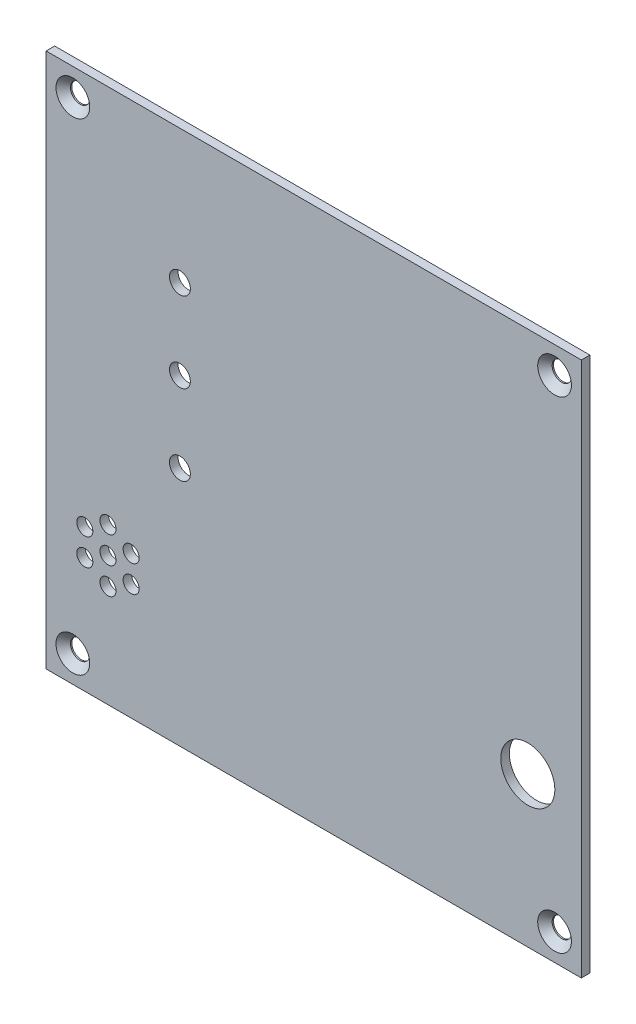
SolidWorks part; units mm, degrees
material "Perspex (TM) Plaque acrylique coulée"
ref_plane "Plan de face" through (0, 0, 0) normal (0, 0, 1) x (1, 0, 0)
ref_plane "Plan de dessus" through (0, 0, 0) normal (0, 1, 0) x (1, 0, 0)
ref_plane "Plan de droite" through (0, 0, 0) normal (1, 0, 0) x (0, 0, -1)
sketch "Esquisse1" plane through (0, 0, 0) normal (0, 0, 1) x (1, 0, 0)
  line L1 (0, 0) -> (100, 0)
  line L2 (0, 0) -> (0, 100)
  line L3 (0, 100) -> (100, 100)
  line L4 (100, 0) -> (100, 100)
  dimension "D1" = 100
  dimension "D2" = 100
extrude "Boss.-Extru.1" add sketch "Esquisse1" along normal blind 1.6
hole_wizard "Fraisage pour vis à tête fraisée M31" positions "Esquisse3D1" profile "Esquisse3" countersink size "M3" standard "ISO" end condition through all
sketch3d "Esquisse3D1"
  line L0 (100, 100, 1.6) -> (0, 100, 1.6) construction
  line L1 (0, 100, 1.6) -> (0, 0, 1.6) construction
  line L2 (100, 0, 1.6) -> (100, 100, 1.6) construction
  line L3 (0, 0, 1.6) -> (100, 0, 1.6) construction
  point P0 (5, 95, 1.6)
  point P2 (95, 95, 1.6)
  point P4 (95, 5, 1.6)
  point P6 (5, 5, 1.6)
  dimension "D1" = 5
  dimension "D2" = 5
  dimension "D3" = 5
  dimension "D4" = 5
  dimension "D5" = 5
  dimension "D6" = 5
  dimension "D7" = 5
  dimension "D8" = 5
sketch "Esquisse3" plane through (5, 95, 1.6) normal (1, 0, 0) x (0, -1, 0)
  line L0 (0, 0) -> (0, 1.6)
  line L1 (0, 1.6) -> (1.8, 1.6)
  line L2 (1.8, 1.6) -> (1.8, 1.35)
  line L3 (1.8, 1.35) -> (3.15, 0)
  line L5 (3.15, 0) -> (0, 0)
  line L6 (-1.8, 1.35) -> (-3.15, 0) construction
  line L11 (0, -6.35) -> (0, 107.95) construction
  dimension "Diamètre du perçage jusqu'au prochain" = 3.6
  dimension "Profondeur du perçage jusqu'au prochain" = 1.6
  dimension "Diamètre du fraisage entrant" = 6.3
  dimension "Angle du fraisage entrant" = 90
sketch "Esquisse4" plane through (0, 0, 1.6) normal (0, 0, 1) x (1, 0, 0)
  line L0 (0, 0) -> (100, 0) construction
  line L1 (100, 0) -> (100, 100) construction
  line L2 (0, 100) -> (0, 0) construction
  circle A0 centre (90, 28) radius 5.05
  circle A1 centre (11.557, 24.13) radius 1.5
  circle A3 centre (11.557, 29.13) radius 1.5
  circle A4 centre (15.8871, 26.63) radius 1.5
  circle A5 centre (15.8871, 21.63) radius 1.5
  circle A6 centre (11.557, 19.13) radius 1.5
  circle A7 centre (7.2269, 21.63) radius 1.5
  circle A8 centre (7.2269, 26.63) radius 1.5
  circle A9 centre (25, 75) radius 1.95
  circle A10 centre (25, 60) radius 1.95
  circle A11 centre (25, 45) radius 1.95
  point P25 (11.557, 24.13)
  dimension "D1" = 28
  dimension "D3" = 11.557
  dimension "D5" = 6
  dimension "D7" = 25
  dimension "D10" = 3
  dimension "D2" = 10
  dimension "D4" = 24.13
  dimension "D6" = 11.557
  dimension "D8" = 75
  dimension "D9" = 29.13
extrude "Enlèv. mat.-Extru.1" cut sketch "Esquisse4" against normal through all
sketch "Esquisse5" plane through (0, 0, 1.6) normal (0, 0, 1) x (1, 0, 0)
  line L0 (0, 100) -> (0, 0) construction
  line L1 (100, 0) -> (100, 100) construction
  line L2 (0, 0) -> (100, 0) construction
  text T0 "OCCUPÉ" font "Arial" height 3.5
  text T1 "ATTENDEZ" font "Arial" height 3.5
  text T2 "ENTREZ" font "Arial" height 3.5
  text T3 "SONNETTE" font "Arial" height in points 28
  dimension "D7" = 80
  dimension "D1" = 30
  dimension "D2" = 73
  dimension "D3" = 58
  dimension "D4" = 30
  dimension "D5" = 30
  dimension "D6" = 43
  dimension "D8" = 5
sketch "Esquisse6" plane through (0, 0, 1.6) normal (0, 0, 1) x (1, 0, 0)
  line L7 (0, 0) -> (100, 0) construction
  line L8 (100, 0) -> (100, 100) construction
  text T0 "ö" font "Wingdings" height in points 48
  dimension "D1" = 11
  dimension "D2" = 27
